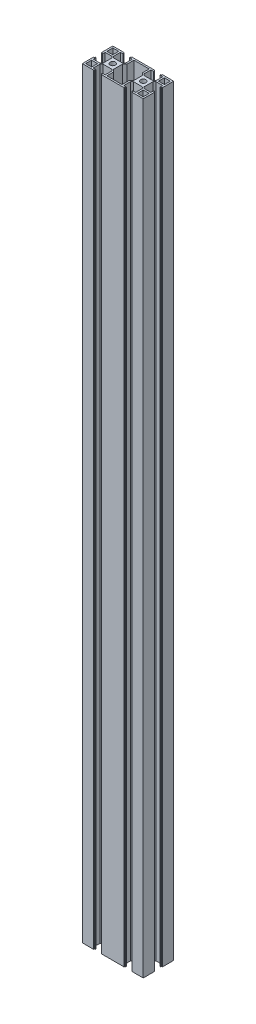
SolidWorks part; units mm, degrees
ref_plane "Front Plane" through (0, 0, 0) normal (0, 0, 1) x (1, 0, 0)
ref_plane "Top Plane" through (0, 0, 0) normal (0, 1, 0) x (1, 0, 0)
ref_plane "Right Plane" through (0, 0, 0) normal (1, 0, 0) x (0, 0, -1)
sketch "Sketch1" plane through (0, 0, 0) normal (0, 1, 0) x (1, 0, 0)
  line L0 (0, 20) -> (0, -20) construction
  line L1 (-40, -20) -> (40, -20)
  line L2 (-40, -20) -> (-40, 20)
  line L3 (-40, 20) -> (40, 20)
  line L4 (40, -20) -> (40, 20)
  line L5 (-40, -20) -> (40, 20) construction
  line L6 (-40, 20) -> (40, -20) construction
  line L7 (-40, 20) -> (0, -20) construction
  line L8 (0, 20) -> (-40, -20) construction
  line L9 (-40, 0) -> (0, 0) construction
  line L10 (-27.8, -17.8) -> (-12.2, -17.8)
  line L11 (-12.2, -17.8) -> (-12.2, -8.925)
  line L12 (-12.2, -8.925) -> (-14.125, -7)
  line L13 (-14.125, -7) -> (-25.875, -7)
  line L14 (-25.875, -7) -> (-27.8, -8.925)
  line L15 (-27.8, -8.925) -> (-27.8, -17.8)
  line L16 (-28.925, -7.8) -> (-37.8, -7.8)
  line L17 (-27, -5.875) -> (-28.925, -7.8)
  line L18 (-27, 5.875) -> (-27, -5.875)
  line L19 (-28.925, 7.8) -> (-27, 5.875)
  line L20 (-37.8, 7.8) -> (-28.925, 7.8)
  line L21 (-37.8, -7.8) -> (-37.8, 7.8)
  line L22 (-27.8, 8.925) -> (-27.8, 17.8)
  line L23 (-25.875, 7) -> (-27.8, 8.925)
  line L24 (-14.125, 7) -> (-25.875, 7)
  line L25 (-12.2, 8.925) -> (-14.125, 7)
  line L26 (-12.2, 17.8) -> (-12.2, 8.925)
  line L27 (-27.8, 17.8) -> (-12.2, 17.8)
  line L28 (-20, 20) -> (-20, -20) construction
  line L29 (27.8, 17.8) -> (12.2, 17.8)
  line L30 (12.2, 17.8) -> (12.2, 8.925)
  line L31 (12.2, 8.925) -> (14.125, 7)
  line L32 (14.125, 7) -> (25.875, 7)
  line L33 (25.875, 7) -> (27.8, 8.925)
  line L34 (27.8, 8.925) -> (27.8, 17.8)
  line L35 (37.8, -7.8) -> (37.8, 7.8)
  line L36 (37.8, 7.8) -> (28.925, 7.8)
  line L37 (28.925, 7.8) -> (27, 5.875)
  line L38 (27, 5.875) -> (27, -5.875)
  line L39 (27, -5.875) -> (28.925, -7.8)
  line L40 (28.925, -7.8) -> (37.8, -7.8)
  line L41 (27.8, -8.925) -> (27.8, -17.8)
  line L42 (25.875, -7) -> (27.8, -8.925)
  line L43 (14.125, -7) -> (25.875, -7)
  line L44 (12.2, -8.925) -> (14.125, -7)
  line L45 (12.2, -17.8) -> (12.2, -8.925)
  line L46 (27.8, -17.8) -> (12.2, -17.8)
  point P0 (0, 0)
  point P30 (-20, 0)
  point P31 (-20, 17.8)
  dimension "D1" = 80
  dimension "D2" = 40
  dimension "D3" = 10.8
  dimension "D4" = 11.75
  dimension "D5" = 15.6
  dimension "D6" = 2.2
extrude "Boss-Extrude1" add sketch "Sketch1" along normal blind 1000
sketch "Sketch2" plane through (0, 1000, 0) normal (0, 1, 0) x (1, 0, 0)
  line L0 (0, -20) -> (0, 20) construction
  line L1 (-40, -20) -> (40, -20) construction
  line L2 (40, 20) -> (-40, 20) construction
  line L3 (-20, -20) -> (-20, 20) construction
  line L4 (-37.8, 7.8) -> (-37.8, -7.8) construction
  line L5 (-37.8, -7.8) -> (-28.925, -7.8) construction
  line L6 (-28.925, -7.8) -> (-27, -5.875) construction
  line L7 (-27, -5.875) -> (-27, 5.875) construction
  line L8 (-27, 5.875) -> (-28.925, 7.8) construction
  line L9 (-28.925, 7.8) -> (-37.8, 7.8) construction
  line L10 (-37.8, 7.8) -> (-37.8, -7.8)
  line L11 (-37.8, -7.8) -> (-28.925, -7.8)
  line L12 (-28.925, -7.8) -> (-27, -5.875)
  line L13 (-27, -5.875) -> (-27, 5.875)
  line L14 (-27, 5.875) -> (-28.925, 7.8)
  line L15 (-28.925, 7.8) -> (-37.8, 7.8)
  line L16 (-10, 7.8) -> (-2.2, 7.8) construction
  line L17 (-13, 5.875) -> (-10, 8.875)
  line L18 (-13, -5.875) -> (-13, 5.875)
  line L19 (-10, -8.875) -> (-13, -5.875)
  line L20 (-2.2, -7.8) -> (-11.075, -7.8) construction
  line L21 (-2.2, 7.8) -> (-2.2, -7.8) construction
  line L22 (2.2, 7.8) -> (2.2, -7.8) construction
  line L23 (2.2, -7.8) -> (11.075, -7.8) construction
  line L24 (10, -8.875) -> (13, -5.875)
  line L25 (13, -5.875) -> (13, 5.875)
  line L26 (13, 5.875) -> (10, 8.875)
  line L27 (11.075, 7.8) -> (2.2, 7.8) construction
  line L28 (-10, 17.8) -> (10, 17.8)
  line L29 (37.8, 17.8) -> (30, 10) construction
  line L30 (-10, -17.8) -> (10, -17.8)
  line L31 (37.8, 10) -> (30, 17.8) construction
  line L32 (-10, 17.8) -> (-10, 8.875)
  line L33 (-12.2, 8.925) -> (-12.2, 17.8) construction
  line L34 (10, 17.8) -> (10, 8.875)
  line L35 (-40, 0) -> (40, 0) construction
  line L36 (-40, 20) -> (-40, -20) construction
  line L37 (40, -20) -> (40, 20) construction
  line L38 (10, -17.8) -> (10, -8.875)
  line L39 (-10, -17.8) -> (-10, -8.875)
  line L40 (-10, -17.8) -> (10, -17.8)
  line L41 (-27.8, 17.8) -> (-27.8, 8.925) construction
  line L42 (-37.8, 10) -> (-30, 10)
  line L43 (-37.8, 10) -> (-37.8, 17.8)
  line L44 (-37.8, 17.8) -> (-30, 17.8)
  line L45 (-30, 10) -> (-30, 17.8)
  line L46 (-37.8, 10) -> (-30, 17.8) construction
  line L47 (-37.8, 17.8) -> (-30, 10) construction
  line L48 (30, 10) -> (30, 17.8)
  line L49 (37.8, 17.8) -> (30, 17.8)
  line L50 (37.8, 10) -> (37.8, 17.8)
  line L51 (37.8, 10) -> (30, 10)
  line L52 (-37.8, -17.8) -> (-30, -10) construction
  line L53 (-37.8, -10) -> (-30, -17.8) construction
  line L54 (-30, -10) -> (-30, -17.8)
  line L55 (-37.8, -17.8) -> (-30, -17.8)
  line L56 (-37.8, -10) -> (-37.8, -17.8)
  line L57 (-37.8, -10) -> (-30, -10)
  line L58 (37.8, -10) -> (30, -17.8) construction
  line L59 (37.8, -17.8) -> (30, -10) construction
  line L60 (37.8, -10) -> (30, -10)
  line L61 (37.8, -10) -> (37.8, -17.8)
  line L62 (37.8, -17.8) -> (30, -17.8)
  line L63 (30, -10) -> (30, -17.8)
  line L64 (14.125, -7) -> (12.2, -8.925) construction
  point P32 (-33.9, 13.9)
  point P53 (33.9, 13.9)
  point P58 (-33.9, -13.9)
  point P63 (33.9, -13.9)
  dimension "D1" = 20
  dimension "D2" = 2.2
  dimension "D3" = 2.2
  dimension "D4" = 2.2
  dimension "D5" = 2.2
  dimension "D6" = 2.2
  dimension "D7" = 2.2
extrude "Cut-Extrude1" cut sketch "Sketch2" against normal through all contours L60 L63 L62 L61 | L39 L30 L38 L24 L25 L26 L34 L28 L32 L17 L18 L19 | L51 L50 L49 L48 | L57 L56 L55 L54 | L42 L45 L44 L43
sketch "Sketch3" plane through (0, 1000, 0) normal (0, 1, 0) x (1, 0, 0)
  line L0 (-25.1, 20) -> (-25.1, 18.9)
  line L1 (40, 20) -> (-40, 20) construction
  line L2 (-25.1, 18.9) -> (-24.1, 18.9)
  line L3 (-24.1, 18.9) -> (-24.1, 17.8)
  line L4 (-12.2, 17.8) -> (-27.8, 17.8) construction
  line L5 (-20, 20) -> (-20, 17.8) construction
  line L6 (-12.2, 8.925) -> (-12.2, 17.8) construction
  line L7 (-15.9, 18.9) -> (-15.9, 17.8)
  line L8 (-14.9, 18.9) -> (-15.9, 18.9)
  line L9 (-14.9, 20) -> (-14.9, 18.9)
  line L10 (-25.1, 20) -> (-14.9, 20)
  line L11 (-24.1, 17.8) -> (-15.9, 17.8)
  line L12 (-20, 7) -> (-20, -7) construction
  line L13 (-25.875, 7) -> (-14.125, 7) construction
  line L14 (-14.125, -7) -> (-25.875, -7) construction
  line L15 (-40, 20) -> (0, -20) construction
  line L16 (-40, -20) -> (40, -20) construction
  line L17 (-40, 0) -> (-37.8, 0) construction
  line L18 (-37.8, 4.1) -> (-37.8, -4.1)
  line L19 (-40, 5.1) -> (-40, -5.1)
  line L20 (-40, -5.1) -> (-38.9, -5.1)
  line L21 (-38.9, -5.1) -> (-38.9, -4.1)
  line L22 (-38.9, -4.1) -> (-37.8, -4.1)
  line L23 (-38.9, 4.1) -> (-37.8, 4.1)
  line L24 (-38.9, 5.1) -> (-38.9, 4.1)
  line L25 (-40, 5.1) -> (-38.9, 5.1)
  line L26 (-20, -20) -> (-20, -17.8) construction
  line L27 (-24.1, -17.8) -> (-15.9, -17.8)
  line L28 (-25.1, -20) -> (-14.9, -20)
  line L29 (-14.9, -20) -> (-14.9, -18.9)
  line L30 (-14.9, -18.9) -> (-15.9, -18.9)
  line L31 (-15.9, -18.9) -> (-15.9, -17.8)
  line L32 (-24.1, -18.9) -> (-24.1, -17.8)
  line L33 (-25.1, -18.9) -> (-24.1, -18.9)
  line L34 (-25.1, -20) -> (-25.1, -18.9)
  line L35 (0, -20) -> (0, 20) construction
  line L36 (20, -20) -> (20, -17.8) construction
  line L37 (40, 0) -> (37.8, 0) construction
  line L38 (20, 7) -> (20, -7) construction
  line L39 (20, 20) -> (20, 17.8) construction
  line L40 (25.1, -20) -> (25.1, -18.9)
  line L41 (25.1, -18.9) -> (24.1, -18.9)
  line L42 (24.1, -18.9) -> (24.1, -17.8)
  line L43 (15.9, -18.9) -> (15.9, -17.8)
  line L44 (14.9, -18.9) -> (15.9, -18.9)
  line L45 (14.9, -20) -> (14.9, -18.9)
  line L46 (25.1, -20) -> (14.9, -20)
  line L47 (24.1, -17.8) -> (15.9, -17.8)
  line L48 (40, 5.1) -> (38.9, 5.1)
  line L49 (38.9, 5.1) -> (38.9, 4.1)
  line L50 (38.9, 4.1) -> (37.8, 4.1)
  line L51 (38.9, -4.1) -> (37.8, -4.1)
  line L52 (38.9, -5.1) -> (38.9, -4.1)
  line L53 (40, -5.1) -> (38.9, -5.1)
  line L54 (40, 5.1) -> (40, -5.1)
  line L55 (37.8, 4.1) -> (37.8, -4.1)
  line L56 (24.1, 17.8) -> (15.9, 17.8)
  line L57 (25.1, 20) -> (14.9, 20)
  line L58 (14.9, 20) -> (14.9, 18.9)
  line L59 (14.9, 18.9) -> (15.9, 18.9)
  line L60 (15.9, 18.9) -> (15.9, 17.8)
  line L61 (24.1, 18.9) -> (24.1, 17.8)
  line L62 (25.1, 18.9) -> (24.1, 18.9)
  line L63 (25.1, 20) -> (25.1, 18.9)
  circle A0 centre (-20, 0) radius 3.5
  circle A1 centre (20, 0) radius 3.5
  point P12 (-24.1, 18.35)
  dimension "D5" = 7
  dimension "D1" = 7.8
  dimension "D2" = 1.1
  dimension "D3" = 1
  dimension "D4" = 4.1
extrude "Cut-Extrude2" cut sketch "Sketch3" against normal through all
